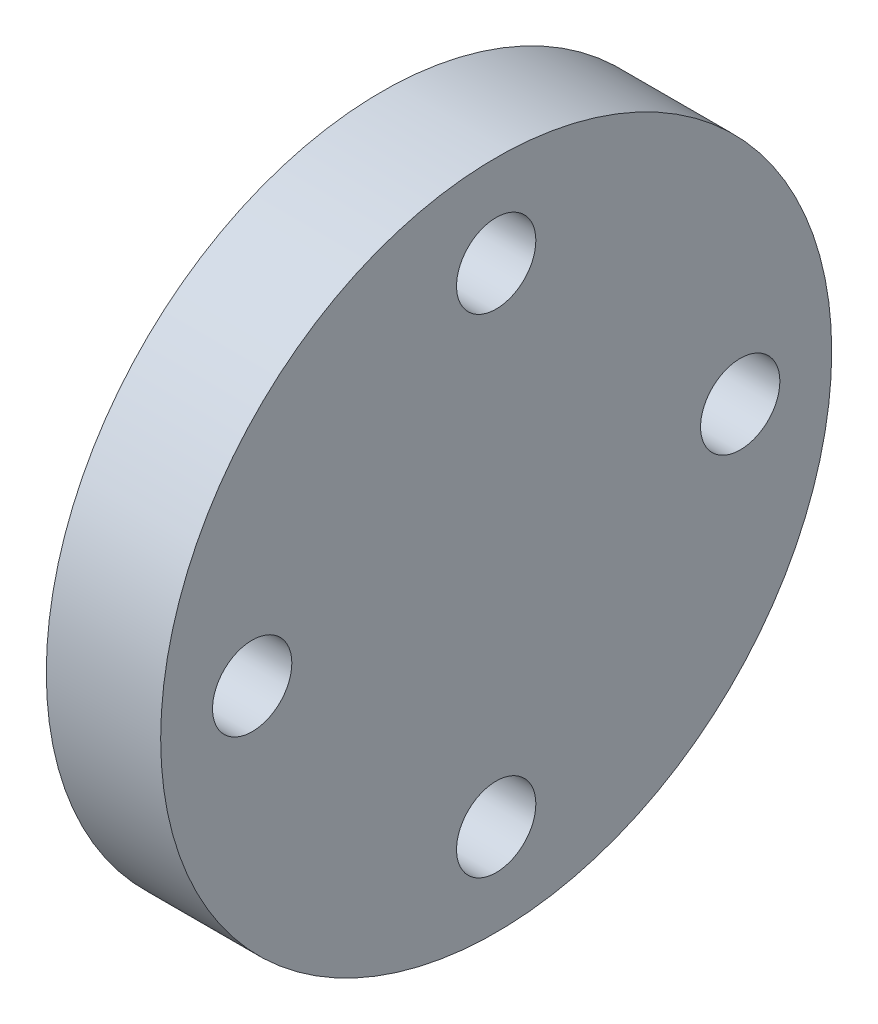
SolidWorks part; units mm, degrees
ref_plane "Front Plane" through (0, 0, 0) normal (0, 0, 1) x (1, 0, 0)
ref_plane "Top Plane" through (0, 0, 0) normal (0, 1, 0) x (1, 0, 0)
ref_plane "Right Plane" through (0, 0, 0) normal (1, 0, 0) x (0, 0, -1)
sketch "Sketch1" plane through (0, 0, 0) normal (1, 0, 0) x (0, 0, -1)
  circle A0 centre (0, 0) radius 13.97
  circle A1 centre (-10.16, 0) radius 1.651
  circle A2 centre (0, 10.16) radius 1.651
  circle A3 centre (10.16, 0) radius 1.651
  circle A4 centre (0, -10.16) radius 1.651
  point P14 (0, 0)
  dimension "D1" = 27.94
  dimension "D2" = 3.302
  dimension "D4" = 4
  dimension "D3" = 10.16
extrude "Boss-Extrude1" add sketch "Sketch1" along normal blind 4.7625
